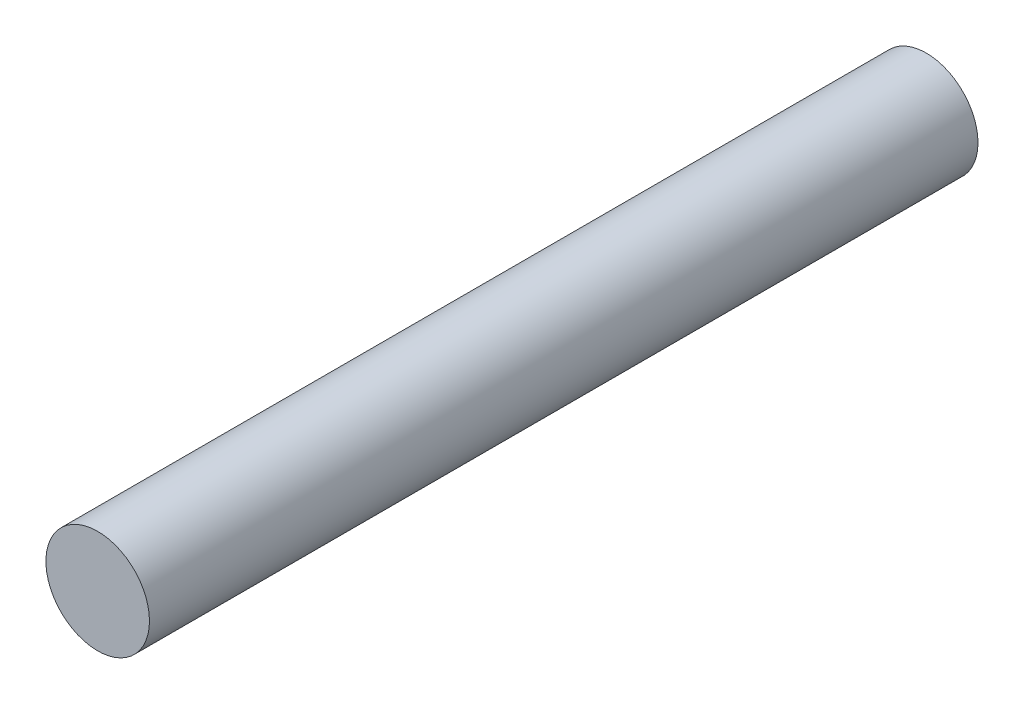
SolidWorks part; units mm, degrees
ref_plane "Front Plane" through (0, 0, 0) normal (0, 0, 1) x (1, 0, 0)
ref_plane "Top Plane" through (0, 0, 0) normal (0, 1, 0) x (1, 0, 0)
ref_plane "Right Plane" through (0, 0, 0) normal (1, 0, 0) x (0, 0, -1)
sketch "Sketch1" plane through (0, 0, 0) normal (0, 0, 1) x (1, 0, 0)
  circle A0 centre (0, 0) radius 3.175
  dimension "D1" = 6.35
extrude "Boss-Extrude1" add sketch "Sketch1" along normal mid plane 50.8
